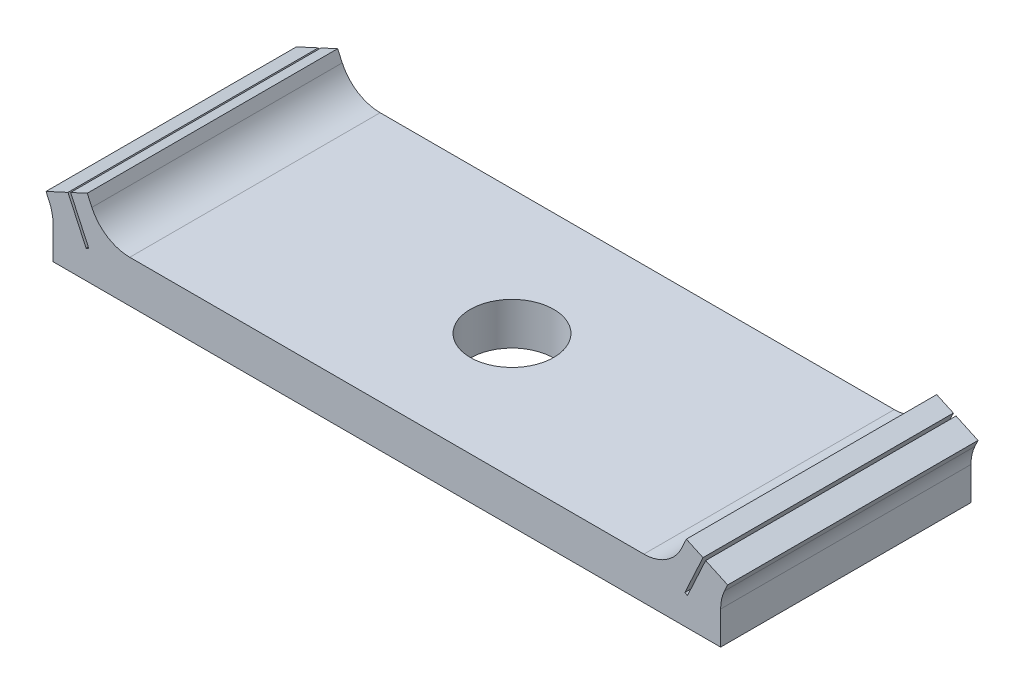
SolidWorks part; units mm, degrees
ref_plane "Front Plane" through (0, 0, 0) normal (0, 0, 1) x (1, 0, 0)
ref_plane "Top Plane" through (0, 0, 0) normal (0, 1, 0) x (1, 0, 0)
ref_plane "Right Plane" through (0, 0, 0) normal (1, 0, 0) x (0, 0, -1)
sketch "Sketch1" plane through (0, 0, 0) normal (0, 0, 1) x (1, 0, 0)
  line L0 (40, 2.5288) -> (40.8383, 4.3447)
  line L1 (-40, -2.5288) -> (40, -2.5288)
  line L2 (-40, -2.5288) -> (-40, 2.5288)
  line L3 (-40, 2.5288) -> (40, 2.5288)
  line L4 (40, -2.5288) -> (40, 2.5288)
  line L5 (-40, -2.5288) -> (40, 2.5288) construction
  line L6 (-40, 2.5288) -> (40, -2.5288) construction
  line L7 (40.8383, 4.3447) -> (35.8923, 6.6279)
  line L8 (35.8923, 6.6279) -> (34, 2.5288)
  line L9 (37.8875, 5.7069) -> (35.708, 0.9857)
  line L10 (35.708, 0.9857) -> (36.0258, 0.839)
  line L11 (36.0258, 0.839) -> (38.2053, 5.5602)
  line L12 (0, 0) -> (0, -50000) construction
  line L13 (-40, 2.5288) -> (-40.8383, 4.3447)
  line L14 (-35.708, 0.9857) -> (-36.0258, 0.839)
  line L15 (-36.0258, 0.839) -> (-38.2053, 5.5602)
  line L16 (-37.8875, 5.7069) -> (-35.708, 0.9857)
  line L17 (-40.8383, 4.3447) -> (-35.8923, 6.6279)
  line L18 (-35.8923, 6.6279) -> (-34, 2.5288)
  point P0 (0, 0)
  dimension "D1" = 65.22
  dimension "D2" = 34
  dimension "D3" = 80
  dimension "D5" = 40
  dimension "D6" = 2
  dimension "D7" = 0.35
  dimension "D8" = 2.9
  dimension "D9" = 5.2
extrude "Boss-Extrude1" add sketch "Sketch1" along normal blind 30 contours L3 L16 L14 L15 L2 L1 L4 L11 L10 L9 | L17 L13 L3 L15 | L18 L17 L16 L3 | L9 L7 L8 L3 | L11 L3 L0 L7
fillet "Fillet1" radius 5 4 edges at (40, 2.5288, 15) (-40, 2.5288, 15) (34, 2.5288, 15) (-34, 2.5288, 15)
sketch "Sketch2" plane through (0, 2.5288, 0) normal (0, 1, 0) x (1, 0, 0)
  circle A0 centre (0, -15) radius 5
  point P2 (0, 0)
  dimension "D2" = 10
  dimension "D1" = 15
extrude "Cut-Extrude1" cut sketch "Sketch2" against normal blind 10
